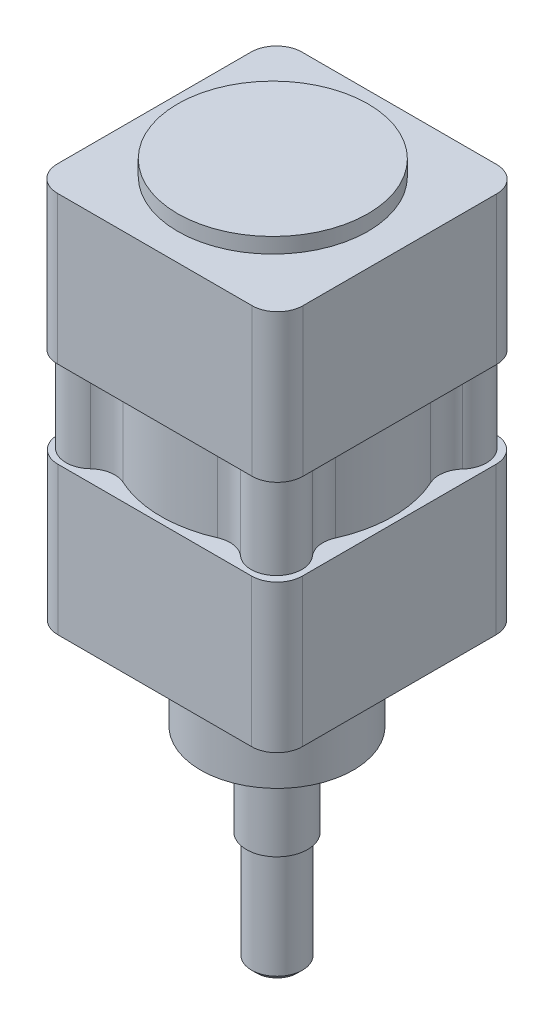
SolidWorks part; units mm, degrees
ref_plane "Alzado" through (0, 0, 0) normal (0, 0, 1) x (1, 0, 0)
ref_plane "Planta" through (0, 0, 0) normal (0, 1, 0) x (1, 0, 0)
ref_plane "Vista lateral" through (0, 0, 0) normal (1, 0, 0) x (0, 0, -1)
sketch "Croquis1" plane through (0, 0, 0) normal (0, 1, 0) x (1, 0, 0)
  line L1 (-19, -24) -> (19, -24)
  line L2 (-24, -19) -> (-24, 19)
  line L3 (-19, 24) -> (19, 24)
  line L4 (24, -19) -> (24, 19)
  line L5 (-24, -24) -> (24, 24) construction
  line L6 (-24, 24) -> (24, -24) construction
  arc A0 (19, -24) -> (24, -19) centre (19, -19) ccw
  arc A1 (-19, -24) -> (-24, -19) centre (-19, -19) cw
  arc A2 (-24, 19) -> (-19, 24) centre (-19, 19) cw
  arc A3 (19, 24) -> (24, 19) centre (19, 19) cw
  point P0 (0, 0)
  dimension "D3" = 5
  dimension "D1" = 48
  dimension "D2" = 48
extrude "Saliente-Extruir1" add sketch "Croquis1" along normal blind 29
sketch "Croquis2" plane through (0, 0, 0) normal (0, -1, 0) x (1, 0, 0)
  circle A0 centre (0, 0) radius 22.77
extrude "Saliente-Extruir2" add sketch "Croquis2" against normal blind 46
sketch "Croquis3" plane through (0, 46, 0) normal (0, 1, 0) x (1, 0, 0)
  circle A0 centre (0, 0) radius 16
  dimension "D1" = 32
extrude "Cortar-Extruir2" cut sketch "Croquis3" against normal blind 90
sketch "Croquis4" plane through (0, 0, 0) normal (0, -1, 0) x (1, 0, 0)
  circle A0 centre (17.8458, 17.9484) radius 5
  circle A1 centre (-18.4612, 17.9484) radius 5
  circle A2 centre (-18.4612, -18.2561) radius 5
  circle A3 centre (17.8458, -18.2561) radius 5
  dimension "D1" = 10
  dimension "D2" = 10
  dimension "D3" = 10
  dimension "D4" = 10
extrude "Saliente-Extruir3" add sketch "Croquis4" against normal blind 65
fillet "Redondeo1" radius 5 8 edges at (12.9114, 37.5, 18.7556) (18.6813, 37.5, 13.0187) (18.4842, 37.5, -13.297) (12.8735, 37.5, -18.7816) (-13.4623, 37.5, -18.3641) (-18.5134, 37.5, -13.2563) (-18.7252, 37.5, 12.9553) (-13.4776, 37.5, 18.3529)
sketch "Croquis5" plane through (0, 46, 0) normal (0, 1, 0) x (1, 0, 0)
  line L1 (-19.1021, -23.9995) -> (19.1021, -23.9995)
  line L2 (-24.1021, -18.9995) -> (-24.1021, 18.9995)
  line L3 (-19.1021, 23.9995) -> (19.1021, 23.9995)
  line L4 (24.1021, -18.9995) -> (24.1021, 18.9995)
  line L5 (-24.1021, -23.9995) -> (24.1021, 23.9995) construction
  line L6 (-24.1021, 23.9995) -> (24.1021, -23.9995) construction
  arc A0 (19.1021, -23.9995) -> (24.1021, -18.9995) centre (19.1021, -18.9995) ccw
  arc A1 (-19.1021, -23.9995) -> (-24.1021, -18.9995) centre (-19.1021, -18.9995) cw
  arc A2 (-24.1021, 18.9995) -> (-19.1021, 23.9995) centre (-19.1021, 18.9995) cw
  arc A3 (19.1021, 23.9995) -> (24.1021, 18.9995) centre (19.1021, 18.9995) cw
  point P0 (0, 0)
  dimension "D1" = 5
extrude "Saliente-Extruir4" add sketch "Croquis5" along normal blind 29
sketch "Croquis6" plane through (0, 75, 0) normal (0, 1, 0) x (1, 0, 0)
  circle A0 centre (-0.8205, 0) radius 18.6764
extrude "Saliente-Extruir5" add sketch "Croquis6" along normal blind 3
sketch "Croquis7" plane through (0, 0, 0) normal (0, 1, 0) x (1, 0, 0)
  circle A0 centre (-16.25, 16.25) radius 3
  circle A1 centre (16.25, 16.25) radius 3
  circle A2 centre (16.25, -16.25) radius 3
  circle A3 centre (-16.25, -16.25) radius 3
  circle A4 centre (0, 0) radius 22.981 construction
  dimension "D1" = 6
  dimension "D2" = 32.5
  dimension "D3" = 32.5
  dimension "D4" = 32.5
  dimension "D5" = 32.5
extrude "Cortar-Extruir3" cut sketch "Croquis7" along normal blind 25
sketch "Croquis8" plane through (0, 0, 0) normal (0, 1, 0) x (1, 0, 0)
  circle A0 centre (0, 0) radius 15
  dimension "D1" = 30
extrude "Saliente-Extruir7" add sketch "Croquis8" against normal blind 18
sketch "Croquis9" plane through (0, -18, 0) normal (0, -1, 0) x (1, 0, 0)
  circle A0 centre (0, 0) radius 6
  dimension "D1" = 12
extrude "Saliente-Extruir9" add sketch "Croquis9" along normal blind 18
sketch "Croquis10" plane through (0, -36, 0) normal (0, -1, 0) x (1, 0, 0)
  circle A0 centre (0, 0) radius 5
  point P3 (0, 0)
  dimension "D1" = 10
extrude "Saliente-Extruir11" add sketch "Croquis10" along normal blind 22
chamfer "Chaflán1" distance 1 angle 45 1 edges at (0, -58, -5)
